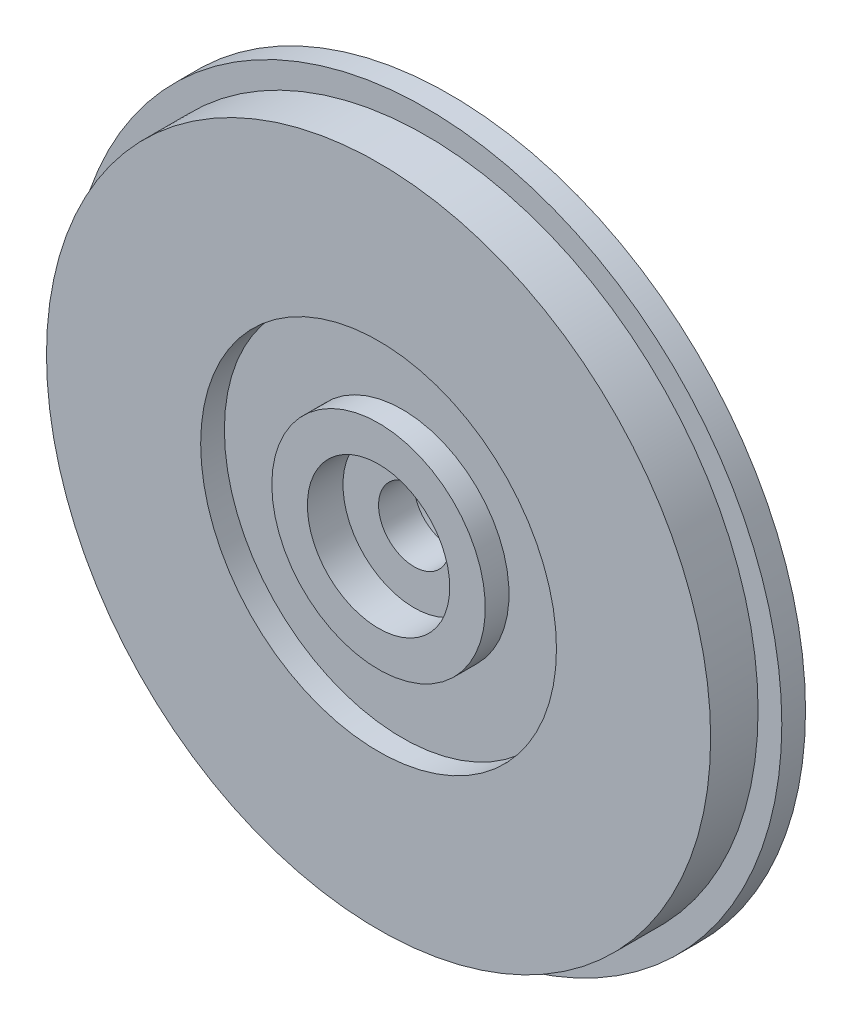
SolidWorks part; units mm, degrees
ref_plane "Front Plane" through (0, 0, 0) normal (0, 0, 1) x (1, 0, 0)
ref_plane "Top Plane" through (0, 0, 0) normal (0, 1, 0) x (1, 0, 0)
ref_plane "Right Plane" through (0, 0, 0) normal (1, 0, 0) x (0, 0, -1)
sketch "Sketch1" plane through (0, 0, 0) normal (0, 1, 0) x (1, 0, 0)
  line L0 (0, -1) -> (4.5, -1)
  line L1 (4.5, -1) -> (4.5, 0)
  line L2 (4.5, 0) -> (7.5, 0)
  line L3 (7.5, 0) -> (7.5, -1)
  line L4 (7.5, -1) -> (14, -1)
  line L5 (14, -1) -> (14, 1)
  line L6 (14, 1) -> (15, 1)
  line L7 (15, 1) -> (15, 2)
  line L8 (15, 2) -> (0, 2)
  line L9 (0, 2) -> (0, -1)
  dimension "D1" = 4.5
  dimension "D2" = 3
  dimension "D3" = 15
  dimension "D4" = 1
  dimension "D5" = 1
  dimension "D6" = 1
  dimension "D7" = 3
revolve "Revolve1" add sketch "Sketch1" angle 360 about L9
sketch "Sketch3" plane through (0, 0, 1) normal (0, 0, 1) x (1, 0, 0)
  circle A0 centre (0, 0) radius 3
extrude "Cut-Extrude1" cut sketch "Sketch3" against normal blind 1.5
sketch "Sketch4" plane through (0, 0, -0.5) normal (0, 0, 1) x (1, 0, 0)
  circle A0 centre (0, 0) radius 1.5
  dimension "D1" = 3
extrude "Cut-Extrude2" cut sketch "Sketch4" against normal through all contours A0
sketch "Sketch5" plane through (0, 0, -2) normal (0, 0, -1) x (-1, 0, 0)
  circle A0 centre (0, 0) radius 4
  dimension "D1" = 8
extrude "Extrude-Thin1" add sketch "Sketch5" along normal blind 2 thin
